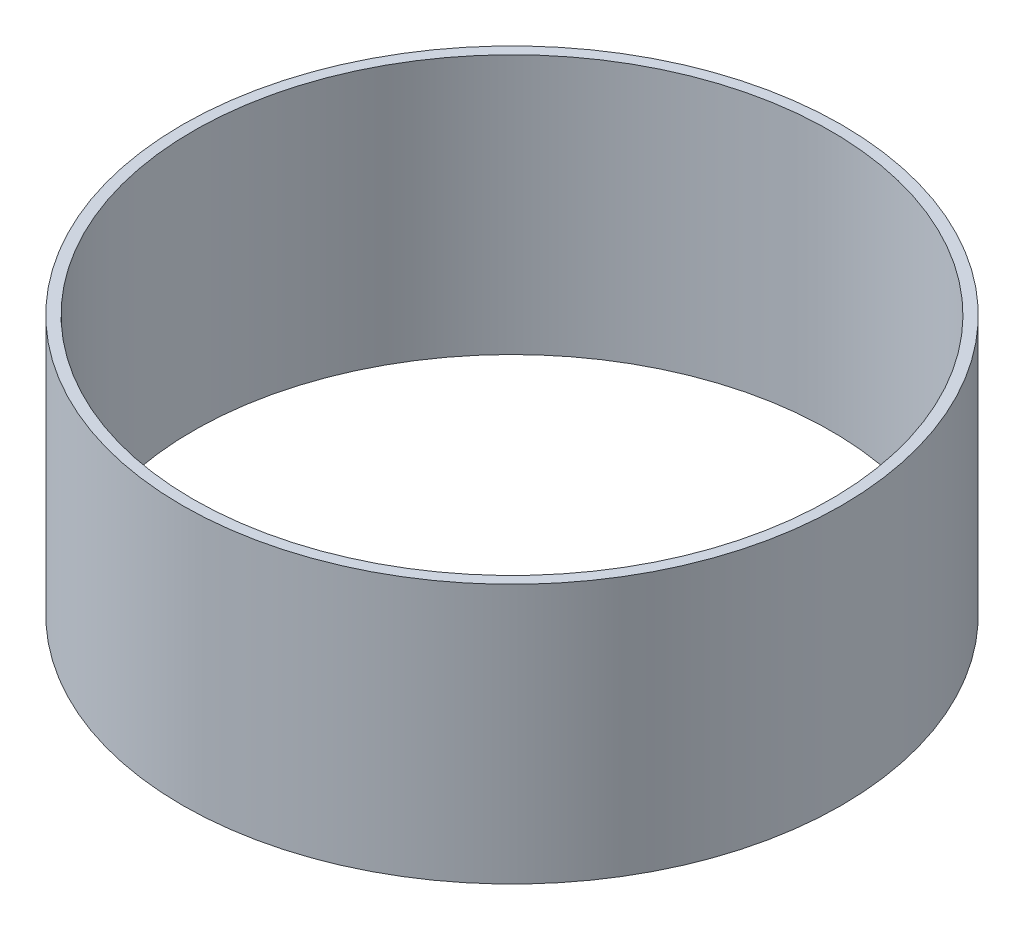
SolidWorks part; units mm, degrees
ref_plane "Plan de face" through (0, 0, 0) normal (0, 0, 1) x (1, 0, 0)
ref_plane "Plan de dessus" through (0, 0, 0) normal (0, 1, 0) x (1, 0, 0)
ref_plane "Plan de droite" through (0, 0, 0) normal (1, 0, 0) x (0, 0, -1)
sketch "Esquisse1" plane through (0, 0, 0) normal (0, 1, 0) x (1, 0, 0)
  circle A0 centre (0, 0) radius 152.4
  circle A1 centre (0, 0) radius 147.4
  dimension "D1" = 304.8
  dimension "D2" = 5
extrude "Boss.-Extru.1" add sketch "Esquisse1" along normal blind 120
